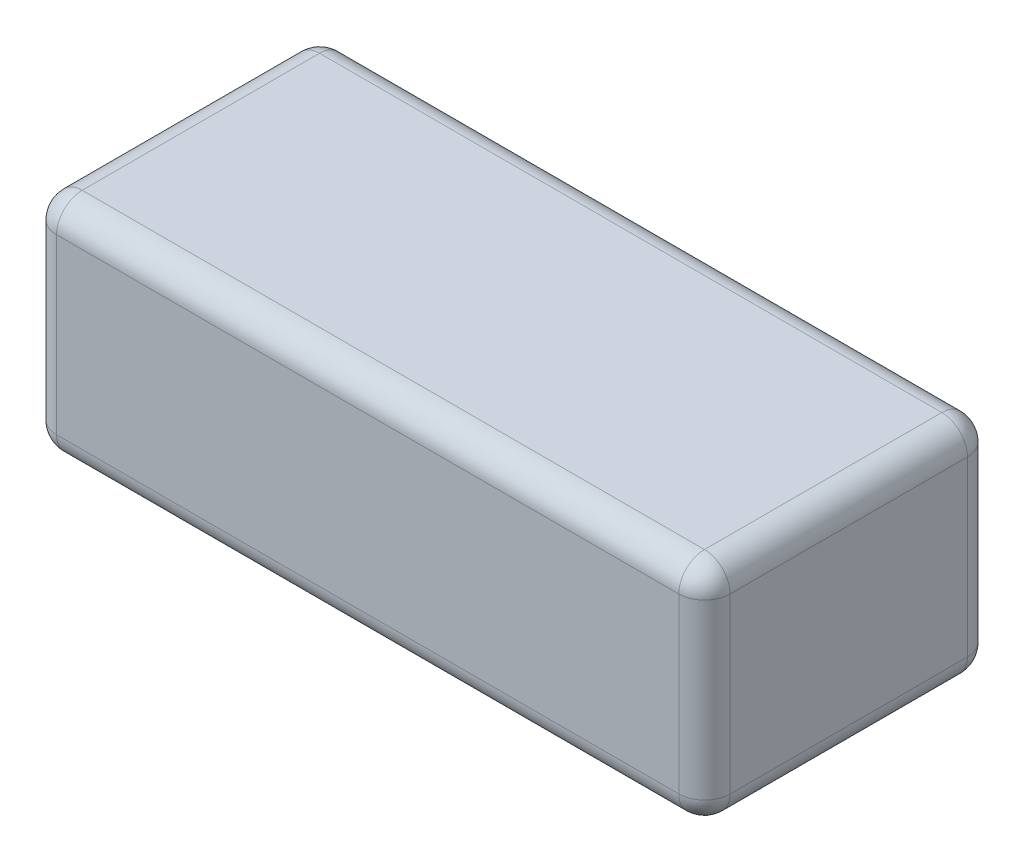
SolidWorks part; units mm, degrees
ref_plane "Front Plane" through (0, 0, 0) normal (0, 0, 1) x (1, 0, 0)
ref_plane "Top Plane" through (0, 0, 0) normal (0, 1, 0) x (1, 0, 0)
ref_plane "Right Plane" through (0, 0, 0) normal (1, 0, 0) x (0, 0, -1)
sketch "Sketch1" plane through (0, 0, 0) normal (0, 1, 0) x (1, 0, 0)
  line L1 (-52.5, 22.5) -> (52.5, 22.5)
  line L2 (-52.5, 22.5) -> (-52.5, -22.5)
  line L3 (-52.5, -22.5) -> (52.5, -22.5)
  line L4 (52.5, 22.5) -> (52.5, -22.5)
  line L5 (-52.5, 22.5) -> (52.5, -22.5) construction
  line L6 (-52.5, -22.5) -> (52.5, 22.5) construction
  point P0 (0, 0)
extrude "Boss-Extrude1" add sketch "Sketch1" along normal blind 35
fillet "Fillet1" radius 4 12 edges at (52.5, 17.5, 22.5) (52.5, 17.5, -22.5) (-52.5, 17.5, -22.5) (-52.5, 17.5, 22.5) (0, 0, -22.5) (-52.5, 0, 0) (0, 0, 22.5) (52.5, 0, 0) (0, 35, 22.5) (-52.5, 35, 0) (0, 35, -22.5) (52.5, 35, 0)
